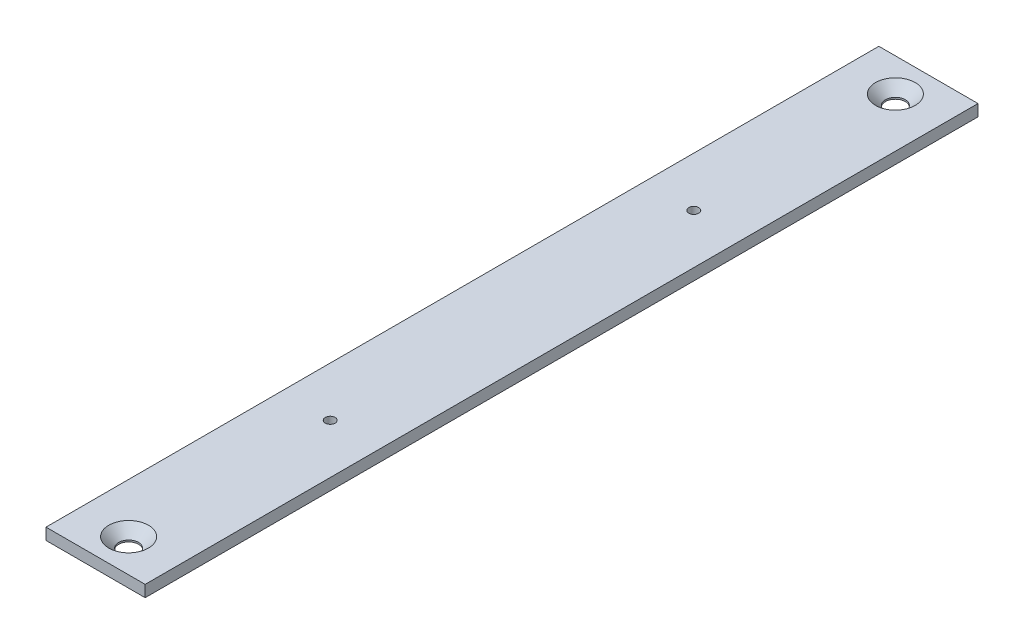
SolidWorks part; units mm, degrees
ref_plane "Front Plane" through (0, 0, 0) normal (0, 0, 1) x (1, 0, 0)
ref_plane "Top Plane" through (0, 0, 0) normal (0, 1, 0) x (1, 0, 0)
ref_plane "Right Plane" through (0, 0, 0) normal (1, 0, 0) x (0, 0, -1)
sketch "Sketch1" plane through (0, 0, 0) normal (0, 1, 0) x (1, 0, 0)
  line L1 (-15, -126) -> (15, -126)
  line L2 (-15, -126) -> (-15, 126)
  line L3 (-15, 126) -> (15, 126)
  line L4 (15, -126) -> (15, 126)
  line L5 (-15, -126) -> (15, 126) construction
  line L6 (-15, 126) -> (15, -126) construction
  point P0 (0, 0)
  dimension "D1" = 30
  dimension "D2" = 252
extrude "Boss-Extrude1" add sketch "Sketch1" along normal blind 3.5
sketch "Sketch2" plane through (0, 3.5, 0) normal (0, 1, 0) x (1, 0, 0)
  line L0 (-15, 0) -> (15, 0) construction
  line L1 (-15, 126) -> (-15, -126) construction
  line L2 (15, -126) -> (15, 126) construction
  line L3 (15, 126) -> (-15, 126) construction
  circle A0 centre (0, 55) radius 1.5
  circle A1 centre (0, -55) radius 1.5
  circle A2 centre (0, 116) radius 3
  circle A3 centre (0, -116) radius 3
  dimension "D1" = 3
  dimension "D2" = 55
  dimension "D4" = 6
  dimension "D3" = 15
  dimension "D5" = 15
  dimension "D6" = 10
extrude "Cut-Extrude1" cut sketch "Sketch2" against normal blind 3.5
chamfer "Chamfer1" distance 3 angle 45 2 edges at (0, 3.5, 113) (0, 3.5, -113)
